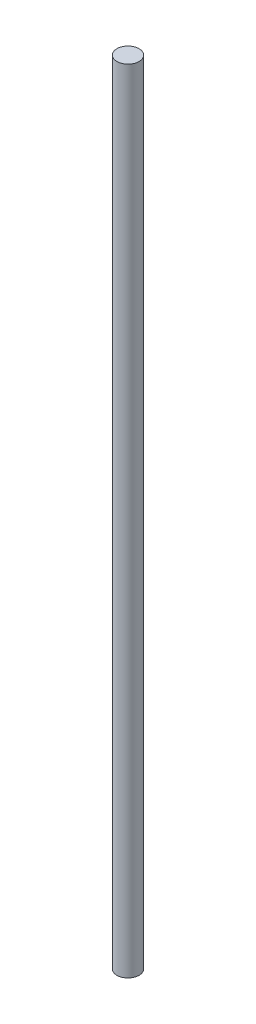
SolidWorks part; units mm, degrees
material "AISI 1020"
ref_plane "Front Plane" through (0, 0, 0) normal (0, 0, 1) x (1, 0, 0)
ref_plane "Top Plane" through (0, 0, 0) normal (0, 1, 0) x (1, 0, 0)
ref_plane "Right Plane" through (0, 0, 0) normal (1, 0, 0) x (0, 0, -1)
sketch "Croquis1" plane through (0, 0, 0) normal (0, 1, 0) x (1, 0, 0)
  line L0 (0, -65) -> (0, -35) construction
  line L1 (50, -65) -> (-50, -65)
  line L2 (50, -65) -> (50, 65)
  line L3 (50, 65) -> (-50, 65)
  line L4 (-50, -65) -> (-50, 65)
  line L5 (50, -65) -> (-50, 65) construction
  line L6 (50, 65) -> (-50, -65) construction
  line L7 (22, -35) -> (-22, -35) construction
  line L8 (23.57, -11.43) -> (-23.57, -58.57) construction
  line L9 (23.57, -58.57) -> (-23.57, -11.43) construction
  line L10 (-23.57, -58.57) -> (23.57, -58.57) construction
  line L11 (23.57, -58.57) -> (23.57, -11.43) construction
  line L12 (0, 65) -> (0, 57) construction
  line L13 (16.5, 57) -> (-16.5, 57)
  line L14 (16.5, 57) -> (33, 57) construction
  line L15 (-16.5, 57) -> (-33, 57) construction
  circle A0 centre (0, -35) radius 11
  circle A1 centre (-22, -35) radius 4
  circle A2 centre (22, -35) radius 4
  circle A3 centre (-23.57, -58.57) radius 2.5
  circle A4 centre (23.57, -58.57) radius 2.5
  circle A5 centre (-23.57, -11.43) radius 2.5
  circle A6 centre (23.57, -11.43) radius 2.5
  circle A7 centre (-33, 57) radius 1.5
  circle A8 centre (-16.5, 57) radius 1.5
  circle A9 centre (0, 57) radius 1.5
  circle A10 centre (16.5, 57) radius 1.5
  circle A11 centre (33, 57) radius 1.5
  point P0 (0, 0)
  point P12 (0, -35)
  point P17 (0, -35)
  point P20 (0, -35)
  point P29 (0, 57)
  dimension "D4" = 22
  dimension "D6" = 8
  dimension "D7" = 47.14
  dimension "D8" = 5
  dimension "D12" = 3
  dimension "D1" = 100
  dimension "D2" = 130
  dimension "D3" = 30
  dimension "D5" = 44
  dimension "D9" = 33
  dimension "D10" = 8
  dimension "D11" = 16.5
sketch "Croquis2" plane through (0, 0, 0) normal (0, 1, 0) x (1, 0, 0)
  line L0 (50, -65) -> (-50, -65) construction
  line L1 (50, -65) -> (50, 65) construction
  line L2 (50, 65) -> (-50, 65) construction
  line L3 (-50, -65) -> (-50, 65) construction
  line L4 (50, -65) -> (-50, -65)
  line L5 (50, -65) -> (50, 65)
  line L6 (50, 65) -> (-50, 65)
  line L7 (-50, -65) -> (-50, 65)
  circle A0 centre (33, 57) radius 1.5 construction
  circle A1 centre (16.5, 57) radius 1.5 construction
  circle A2 centre (-33, 57) radius 1.5 construction
  circle A3 centre (0, 57) radius 1.5 construction
  circle A4 centre (-16.5, 57) radius 1.5 construction
  circle A5 centre (-23.57, -11.43) radius 2.5 construction
  circle A6 centre (23.57, -11.43) radius 2.5 construction
  circle A7 centre (22, -35) radius 4 construction
  circle A8 centre (0, -35) radius 11 construction
  circle A9 centre (-22, -35) radius 4 construction
  circle A10 centre (23.57, -58.57) radius 2.5 construction
  circle A11 centre (-23.57, -58.57) radius 2.5 construction
  circle A12 centre (33, 57) radius 1.5
  circle A13 centre (16.5, 57) radius 1.5
  circle A14 centre (-33, 57) radius 1.5
  circle A15 centre (0, 57) radius 1.5
  circle A16 centre (-16.5, 57) radius 1.5
  circle A17 centre (-23.57, -11.43) radius 2.5
  circle A18 centre (23.57, -11.43) radius 2.5
  circle A19 centre (22, -35) radius 4
  circle A20 centre (0, -35) radius 11
  circle A21 centre (-22, -35) radius 4
  circle A22 centre (23.57, -58.57) radius 2.5
  circle A23 centre (-23.57, -58.57) radius 2.5
  point P0 (-33, 57)
extrude "Saliente-Extruir1" [suppressed] add sketch "Croquis2" along normal blind 15
sketch "Croquis3" plane through (0, 0, 0) normal (0, 1, 0) x (1, 0, 0)
  line L0 (50, -65) -> (-50, -65) construction
  line L1 (50, -65) -> (50, 65) construction
  line L2 (50, 65) -> (-50, 65) construction
  line L3 (-50, -65) -> (-50, 65) construction
  line L4 (50, -65) -> (-50, -65)
  line L5 (50, -65) -> (50, 65)
  line L6 (50, 65) -> (-50, 65)
  line L7 (-50, -65) -> (-50, 65)
  circle A0 centre (-33, 57) radius 1.5 construction
  circle A1 centre (-16.5, 57) radius 1.5 construction
  circle A2 centre (0, 57) radius 1.5 construction
  circle A3 centre (16.5, 57) radius 1.5 construction
  circle A4 centre (33, 57) radius 1.5 construction
  circle A9 centre (-33, 57) radius 1.5
  circle A10 centre (-16.5, 57) radius 1.5
  circle A11 centre (0, 57) radius 1.5
  circle A12 centre (16.5, 57) radius 1.5
  circle A13 centre (33, 57) radius 1.5
  circle A18 centre (0, -35) radius 11 construction
  circle A19 centre (0, -35) radius 11
  circle A20 centre (22, -35) radius 4 construction
  circle A21 centre (-22, -35) radius 4 construction
  circle A22 centre (22, -35) radius 4
  circle A23 centre (-22, -35) radius 4
extrude "Saliente-Extruir2" [suppressed] add sketch "Croquis3" along normal blind 9
sketch "Croquis4" [suppressed] plane through (0, 0, 0) normal (0, 1, 0) x (1, 0, 0)
  line L0 (-50, -65) -> (-50, 65) construction
  line L1 (50, -65) -> (-50, -65) construction
  line L2 (50, 65) -> (-50, 65) construction
  line L3 (50, -65) -> (50, 65) construction
  line L4 (-50, -65) -> (-50, 65)
  line L5 (50, -65) -> (-50, -65)
  line L6 (50, 65) -> (-50, 65)
  line L7 (50, -65) -> (50, 65)
  circle A0 centre (-33, 57) radius 1.5 construction
  circle A1 centre (-16.5, 57) radius 1.5 construction
  circle A2 centre (0, 57) radius 1.5 construction
  circle A4 centre (-22, -35) radius 4 construction
  circle A5 centre (22, -35) radius 4 construction
  circle A6 centre (-33, 57) radius 1.5
  circle A7 centre (-16.5, 57) radius 1.5
  circle A8 centre (0, 57) radius 1.5
  circle A10 centre (-22, -35) radius 4
  circle A11 centre (22, -35) radius 4
  circle A12 centre (16.5, 57) radius 1.5 construction
  circle A13 centre (33, 57) radius 1.5 construction
  circle A14 centre (16.5, 57) radius 1.5
  circle A15 centre (33, 57) radius 1.5
  circle A16 centre (0, -35) radius 4
  point P0 (16.5, 57)
  point P2 (33, 57)
  dimension "D1" = 8
extrude "Saliente-Extruir3" [suppressed] add sketch "Croquis4" against normal blind 6
sketch "Croquis5" plane through (0, 0, 0) normal (0, 0, 1) x (1, 0, 0)
  line L0 (0, 65) -> (0, 23) construction
  line L1 (50, -65) -> (-50, -65)
  line L2 (50, -65) -> (50, 65)
  line L3 (50, 65) -> (-50, 65)
  line L4 (-50, -65) -> (-50, 65)
  line L5 (50, -65) -> (-50, 65) construction
  line L6 (50, 65) -> (-50, -65) construction
  line L7 (0, 23) -> (-22, 23) construction
  line L8 (-22, 23) -> (-22, 50) construction
  line L9 (-34, 59) -> (10, 59) construction
  line L10 (-10, 41) -> (-34, 41) construction
  line L11 (-10, 41) -> (-10, 59) construction
  line L12 (-10, 59) -> (-34, 59) construction
  line L13 (-34, 41) -> (-34, 59) construction
  line L14 (-10, 41) -> (-34, 59) construction
  line L15 (-10, 59) -> (-34, 41) construction
  line L16 (12, 14) -> (-12, 14) construction
  line L17 (12, 14) -> (12, 32) construction
  line L18 (12, 32) -> (-12, 32) construction
  line L19 (-12, 14) -> (-12, 32) construction
  line L20 (12, 14) -> (-12, 32) construction
  line L21 (12, 32) -> (-12, 14) construction
  line L22 (-34, 59) -> (-34, 5) construction
  circle A0 centre (-34, 59) radius 1.5
  circle A1 centre (-10, 59) radius 1.5
  circle A2 centre (-34, 41) radius 1.5
  circle A3 centre (-10, 41) radius 1.5
  circle A4 centre (-12, 32) radius 1.5
  circle A5 centre (-12, 14) radius 1.5
  circle A6 centre (12, 32) radius 1.5
  circle A7 centre (12, 14) radius 1.5
  circle A8 centre (10, 59) radius 1.5
  circle A9 centre (34, 59) radius 1.5
  circle A10 centre (10, 41) radius 1.5
  circle A11 centre (34, 41) radius 1.5
  circle A12 centre (-34, 5) radius 1.5
  circle A13 centre (-34, -13) radius 1.5
  circle A14 centre (-10, -13) radius 1.5
  circle A15 centre (-10, 5) radius 1.5
  circle A16 centre (10, 5) radius 1.5
  circle A17 centre (10, -13) radius 1.5
  circle A18 centre (34, -13) radius 1.5
  circle A19 centre (34, 5) radius 1.5
  point P0 (0, 0)
  dimension "D8" = 3
  dimension "D1" = 130
  dimension "D2" = 100
  dimension "D3" = 42
  dimension "D4" = 22
  dimension "D5" = 27
  dimension "D6" = 24
  dimension "D7" = 18
  dimension "D10" = 44
  dimension "D12" = 54
  dimension "D9" = 2
  dimension "D11" = 2
extrude "Saliente-Extruir4" [suppressed] add sketch "Croquis5" against normal blind 14
sketch "Croquis6" plane through (0, 0, 0) normal (0, 1, 0) x (1, 0, 0)
  circle A0 centre (-22, -35) radius 4 construction
  circle A1 centre (-22, -35) radius 4
extrude "Saliente-Extruir5" add sketch "Croquis6" against normal blind 285
sketch "Croquis7" [suppressed] plane through (0, 0, 0) normal (0, 0, 1) x (1, 0, 0)
  line L0 (50, 65) -> (-50, 65) construction
  line L1 (50, -65) -> (50, 65) construction
  line L2 (-50, -65) -> (50, -65) construction
  line L3 (-50, 65) -> (-50, -65) construction
  line L4 (50, 65) -> (-50, 65)
  line L5 (50, -65) -> (50, 65)
  line L6 (-50, -65) -> (50, -65)
  line L7 (-50, 65) -> (-50, -65)
extrude "Saliente-Extruir6" [suppressed] add sketch "Croquis7" along normal blind 1
sketch "Croquis8" [suppressed] plane through (0, 0, 1) normal (0, 0, 1) x (1, 0, 0)
  line L0 (0, -65) -> (0, 20) construction
  line L1 (-50, -65) -> (50, -65) construction
  line L2 (45, 20) -> (-45, 20) construction
  line L3 (-45, 20) -> (-45, -30) construction
  line L4 (45, 20) -> (45, -30) construction
  line L5 (45, -30) -> (-45, -30) construction
  circle A0 centre (-45, 20) radius 1.5
  circle A1 centre (45, 20) radius 1.5
  circle A2 centre (-45, -30) radius 1.5
  circle A3 centre (45, -30) radius 1.5
  point P8 (0, 20)
  dimension "D3" = 3
  dimension "D1" = 85
  dimension "D2" = 90
  dimension "D4" = 68
extrude "Cortar-Extruir1" [suppressed] cut sketch "Croquis8" against normal blind 10
